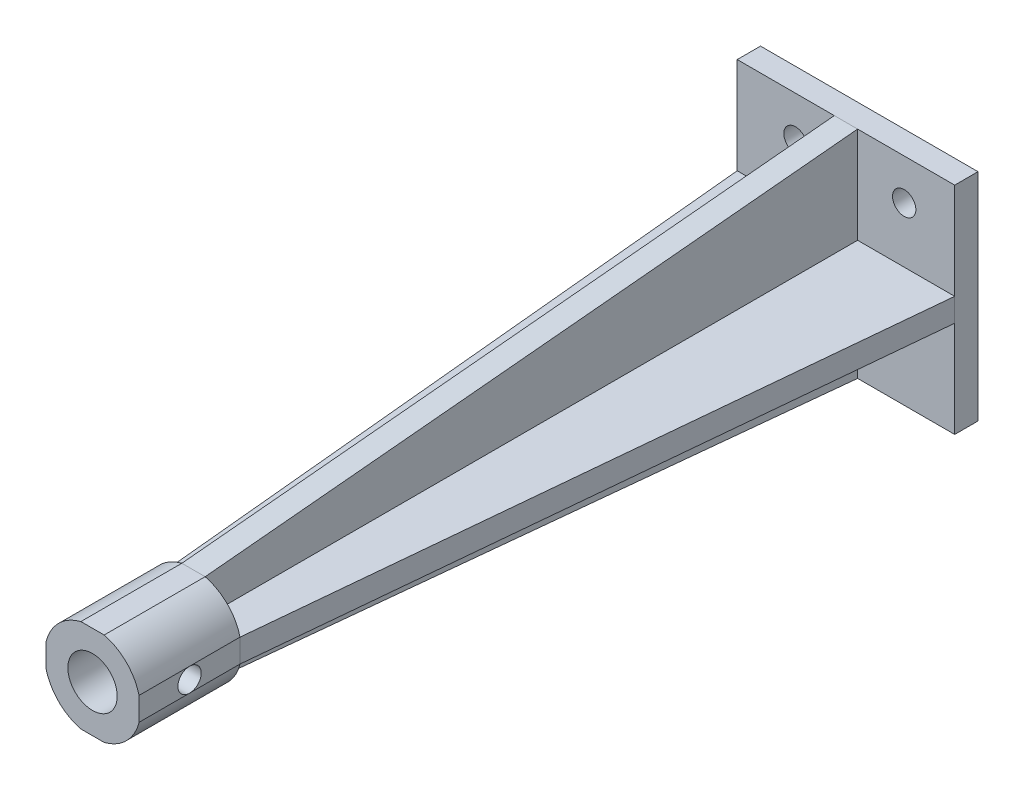
SolidWorks part; units mm, degrees
ref_plane "Alzado" through (0, 0, 0) normal (0, 0, 1) x (1, 0, 0)
ref_plane "Planta" through (0, 0, 0) normal (0, 1, 0) x (1, 0, 0)
ref_plane "Vista lateral" through (0, 0, 0) normal (1, 0, 0) x (0, 0, -1)
sketch "Croquis1" plane through (0, 0, 0) normal (0, 0, 1) x (1, 0, 0)
  line L1 (-19, 26.2422) -> (-47, 26.2422)
  line L2 (-19, 26.2422) -> (-19, -1.5605)
  line L3 (-19, -1.5605) -> (-47, -1.5605)
  line L4 (-47, 26.2422) -> (-47, -1.5605)
  circle A0 centre (-39.5, 7) radius 1.5
  circle A1 centre (-39.5, 21) radius 1.5
  circle A2 centre (-25.5, 21) radius 1.5
  circle A3 centre (-25.5, 7) radius 1.5
extrude "Saliente-Extruir1" add sketch "Croquis1" along normal blind 3
sketch "Croquis2" plane through (0, 0, 0) normal (0, 0, 1) x (1, 0, 0)
  line L0 (-33, 26.2422) -> (-33, -1.5605) construction
  line L1 (-19, 26.2422) -> (-47, 26.2422) construction
  line L2 (-47, -1.5605) -> (-19, -1.5605) construction
  line L3 (-34.5, 26.2422) -> (-34.5, -1.5605)
  line L4 (-31.5, 26.2422) -> (-31.5, -1.5605)
  line L5 (-47, 12.3409) -> (-19, 12.3409) construction
  line L6 (-47, 26.2422) -> (-47, -1.5605) construction
  line L7 (-19, -1.5605) -> (-19, 26.2422) construction
  line L8 (-47, 10.8409) -> (-19, 10.8409)
  line L9 (-47, 13.8409) -> (-19, 13.8409)
  line L10 (-34.5, 26.2422) -> (-31.5, 26.2422)
  line L11 (-34.5, -1.5605) -> (-31.5, -1.5605)
  line L12 (-19, 13.8409) -> (-19, 10.8409)
  line L13 (-47, 13.8409) -> (-47, 10.8409)
  dimension "D1" = 1.5
  dimension "D2" = 1.5
  dimension "D3" = 1.5
  dimension "D4" = 1.5
extrude "Saliente-Extruir2" add sketch "Croquis2" along normal blind 100 contours L3 L11 L4 L8 | L9 L3 L8 L4 | L10 L3 L9 L4 | L12 L9 L4 L8 | L9 L13 L8 L3
sketch "Croquis3" plane through (0, 0, 100) normal (0, 0, 1) x (1, 0, 0)
  line L0 (-33, 26.2422) -> (-33, -1.5605) construction
  line L1 (-34.5, 26.2422) -> (-31.5, 26.2422) construction
  line L2 (-34.5, -1.5605) -> (-31.5, -1.5605) construction
  circle A0 centre (-33, 12.3409) radius 6.175
extrude "Saliente-Extruir3" add sketch "Croquis3" against normal blind 13
sketch "Croquis4" plane through (0, 0, 0) normal (0, 0, 1) x (1, 0, 0)
  line L0 (-33, 26.2422) -> (-33, -1.5605) construction
  line L1 (-34.5, 26.2422) -> (-31.5, 26.2422) construction
  line L2 (-34.5, -1.5605) -> (-31.5, -1.5605) construction
  circle A1 centre (-33, 12.3409) radius 3.175
extrude "Cortar-Extruir6" cut sketch "Croquis4" against normal blind 10 from surface at 100 starting at face at (-33, 12.3409, 100)
sketch "Croquis12" plane through (0, 0, 0) normal (0, 1, 0) x (1, 0, 0)
  line L0 (-47, -3) -> (-38.99, -87)
  line L1 (-38.99, -87) -> (-38.99, -100)
  line L2 (-38.99, -100) -> (-47, -100)
  line L3 (-47, -100) -> (-47, -3) construction
  line L4 (-47, -100) -> (-47, -3)
  line L5 (-19, -3) -> (-19, -100)
  line L6 (-19, -100) -> (-27.01, -100)
  line L7 (-27.01, -100) -> (-27.01, -87)
  line L8 (-27.01, -87) -> (-19, -3)
extrude "Cortar-Extruir7" cut sketch "Croquis12" along normal blind 3 from surface at 10.8409 starting at face at (-25.8367, 10.8409, 63.3333)
sketch "Croquis13" plane through (0, 0, 0) normal (1, 0, 0) x (0, 0, -1)
  line L0 (-100, 18.3309) -> (-87, 18.3309)
  line L1 (-87, 18.3309) -> (-3, 26.2422)
  line L2 (-3, 26.2422) -> (-100, 26.2422)
  line L3 (-100, 26.2422) -> (-100, 18.3309)
  line L4 (-100, -1.5605) -> (-100, 6.3509)
  line L5 (-100, 6.3509) -> (-87, 6.3509)
  line L6 (-87, 6.3509) -> (-3, -1.5605)
  line L7 (-3, -1.5605) -> (-100, -1.5605)
extrude "Cortar-Extruir8" cut sketch "Croquis13" against normal blind 3 from surface at -31.5 starting at face at (-31.5, 19.4714, 63.3333)
sketch "Croquis14" plane through (-38.99, 0, 0) normal (-1, 0, 0) x (0, 0, 1)
  line L0 (87, 12.3409) -> (100, 12.3409) construction
  line L1 (87, 13.8409) -> (87, 10.8409) construction
  line L2 (100, 13.8409) -> (100, 10.8409) construction
  circle A0 centre (93.5, 12.3409) radius 1.5
extrude "Cortar-Extruir9" cut sketch "Croquis14" against normal blind 12
